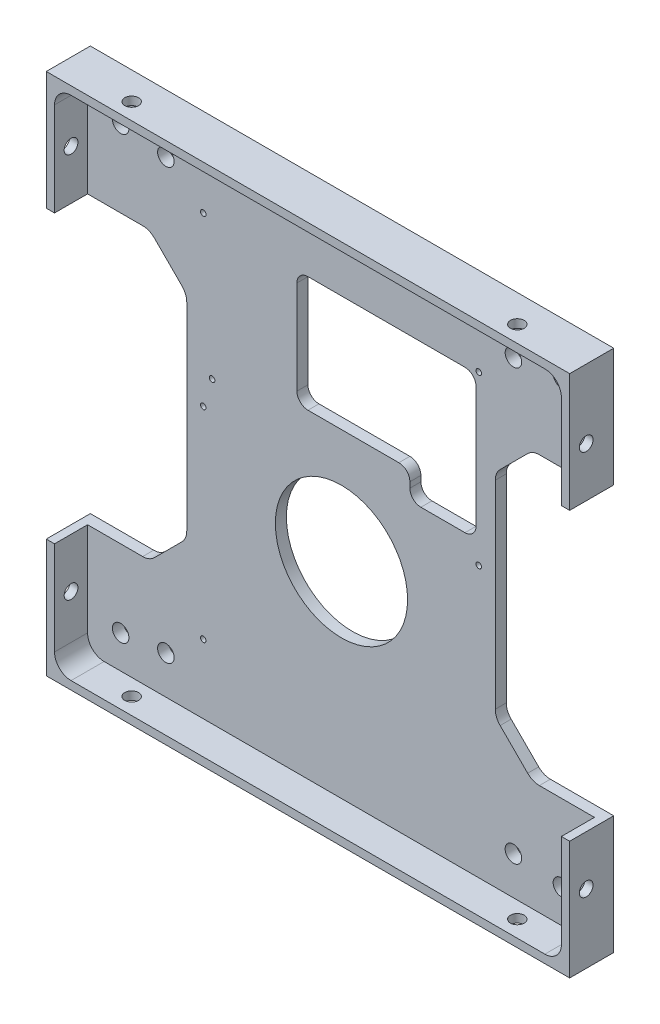
SolidWorks part; units mm, degrees
material "6061-T6 (SS)"
ref_plane "Front" through (0, 0, 0) normal (0, 0, 1) x (1, 0, 0)
ref_plane "Top" through (0, 0, 0) normal (0, 1, 0) x (1, 0, 0)
ref_plane "Right" through (0, 0, 0) normal (1, 0, 0) x (0, 0, -1)
sketch "Sketch1" plane through (0, 0, 0) normal (0, 0, 1) x (1, 0, 0)
  line L1 (-48, -48) -> (48, -48)
  line L2 (-48, -48) -> (-48, 48)
  line L3 (-48, 48) -> (48, 48)
  line L4 (48, -48) -> (48, 48)
  line L5 (-48, -48) -> (48, 48) construction
  line L6 (-48, 48) -> (48, -48) construction
  point P0 (0, 0)
  dimension "D1" = 96
  dimension "D2" = 96
extrude "Boss-Extrude1" add sketch "Sketch1" along normal blind 8
sketch "Sketch2" plane through (0, 0, 8) normal (0, 0, 1) x (1, 0, 0)
  line L1 (46, -46) -> (-46, -46)
  line L2 (46, -46) -> (46, 46)
  line L3 (46, 46) -> (-46, 46)
  line L4 (-46, -46) -> (-46, 46)
  line L5 (46, -46) -> (-46, 46) construction
  line L6 (46, 46) -> (-46, -46) construction
  point P0 (0, 0)
  dimension "D1" = 92
  dimension "D2" = 92
extrude "Component Platform" cut sketch "Sketch2" against normal blind 6
sketch "Sketch3" plane through (0, 0, 2) normal (0, 0, 1) x (1, 0, 0)
  line L1 (-33.8787, -25.1213) -> (-28.8787, -20.1213)
  line L2 (-33.8787, 25.1213) -> (-28.8787, 20.1213)
  line L3 (-28, -18) -> (-28, 18)
  line L4 (-48, -26) -> (-36, -26)
  line L7 (-48, 48) -> (-48, -48) construction
  line L8 (0, -56.7987) -> (0, 73.4321) construction
  line L9 (46, -46) -> (-57.8147, 57.8147) construction
  line L18 (46, 46) -> (-68.5705, -68.5705) construction
  line L23 (-48, 26) -> (-36, 26)
  line L26 (-48, -26) -> (-48, 26)
  line L28 (-48, -48) -> (48, -48) construction
  line L29 (48, -26) -> (48, 26)
  line L30 (48, 26) -> (36, 26)
  line L31 (33.8787, 25.1213) -> (28.8787, 20.1213)
  line L32 (28, -18) -> (28, 18)
  line L33 (33.8787, -25.1213) -> (28.8787, -20.1213)
  line L34 (48, -26) -> (36, -26)
  arc A3 (-28.8787, -20.1213) -> (-28, -18) centre (-31, -18) ccw
  arc A4 (-28.8787, 20.1213) -> (-28, 18) centre (-31, 18) cw
  arc A13 (-33.8787, -25.1213) -> (-36, -26) centre (-36, -23) cw
  arc A15 (-33.8787, 25.1213) -> (-36, 26) centre (-36, 23) ccw
  arc A17 (33.8787, 25.1213) -> (36, 26) centre (36, 23) cw
  arc A18 (28.8787, 20.1213) -> (28, 18) centre (31, 18) ccw
  arc A19 (28.8787, -20.1213) -> (28, -18) centre (31, -18) cw
  arc A20 (33.8787, -25.1213) -> (36, -26) centre (36, -23) ccw
  point P0 (-48, 0)
  point P37 (-48, 0)
  dimension "D2" = 3
  dimension "D3" = 3
  dimension "D4" = 20
  dimension "D6" = 3
  dimension "D7" = 3
  dimension "D8" = 135
  dimension "D5" = 52
  dimension "D9" = 135
  dimension "D10" = 12
  dimension "D11" = 12
  dimension "D12" = 48
extrude "Cable Slots" cut sketch "Sketch3" against normal mid plane 12
ref_plane "Center Y-Plane" through (0, 0, 0) normal (1, 0, 0) x (0, 0, -1)
ref_plane "Center X-Plane" through (0, 0, 0) normal (0, -1, 0) x (-1, 0, 0)
fillet "Inner Corner Fillets" radius 3 4 edges at (46, -46, 5) (-46, -46, 5) (46, 46, 5) (-46, 46, 5)
sketch "Sketch7" plane through (0, 0, 2) normal (0, 0, 1) x (1, 0, 0)
  line L0 (-48, -48) -> (48, -48) construction
  line L4 (48, -48) -> (48, -26) construction
  line L5 (48, 26) -> (48, 48) construction
  line L7 (48, 48) -> (-48, 48) construction
  line L8 (-43, -46) -> (43, -46) construction
  point P1 (-19.32, -29.75)
  point P4 (24.78, -32.85)
  point P5 (24.78, 32.85)
  point P8 (-22.92, 32.85)
  point P12 (24.7, -56.85)
  point P13 (24.7, 48)
  point P14 (-19.4, -48)
  point P15 (48, -32.85)
  point P16 (-48, -32.85)
  point P18 (-19.4, 48)
  point P19 (48, -32.85)
  point P20 (-48, -32.85)
  point P24 (48, 43.7)
  point P25 (-48.7506, 43.7)
  point P27 (48, 32.85)
  point P28 (-23, -48)
  point P29 (-23, 48)
  point P31 (-48.7506, 32.85)
  dimension "D1" = 16.25
  dimension "D2" = 47.7
  dimension "D3" = 15.15
  dimension "D4" = 23.22
  dimension "D5" = 23.22
  dimension "D6" = 44.1
  dimension "D7" = 15.15
  dimension "D8" = 15.15
sketch "Sketch9" plane through (0, 0, 2) normal (0, 0, 1) x (1, 0, 0)
  line L0 (24.5, 31) -> (24.5, 9)
  line L1 (22.5, 33) -> (-6, 33)
  line L2 (22.5, 7) -> (14.5, 7)
  line L5 (-8, 14) -> (-8, 31)
  line L6 (48, 26) -> (48, 48) construction
  line L7 (12.5, 9) -> (12.5, 10)
  line L8 (48, 48) -> (-48, 48) construction
  line L9 (10.5, 12) -> (-6, 12)
  arc A1 (24.5, 9) -> (22.5, 7) centre (22.5, 9) cw
  arc A2 (24.5, 31) -> (22.5, 33) centre (22.5, 31) ccw
  arc A3 (-6, 33) -> (-8, 31) centre (-6, 31) ccw
  arc A8 (-8, 14) -> (-6, 12) centre (-6, 14) ccw
  arc A9 (12.5, 10) -> (10.5, 12) centre (10.5, 10) ccw
  arc A10 (14.5, 7) -> (12.5, 9) centre (14.5, 9) cw
  point P15 (24.5, 33)
  point P18 (-8, 12)
  dimension "D1" = 2
  dimension "D6" = 2
  dimension "D7" = 8
  dimension "D8" = 32.5
  dimension "D2" = 26
  dimension "D3" = 28.5
  dimension "D4" = 15
  dimension "D5" = 23.5
  dimension "D9" = 19
sketch "Sketch11" plane through (48, 0, 0) normal (1, 0, 0) x (0, 0, -1)
  line L0 (-5, -48) -> (-5, 48) construction
  line L1 (-8, -48) -> (0, -48) construction
  line L2 (-8, 48) -> (0, 48) construction
  line L3 (-8, -48) -> (-8, -26) construction
  dimension "D1" = 3
sketch "Sketch12" plane through (0, 48, 0) normal (0, 1, 0) x (1, 0, 0)
  line L0 (-48, -5) -> (48, -5) construction
  line L1 (-48, -8) -> (-48, 0) construction
  line L2 (48, -8) -> (48, 0) construction
  line L3 (48, -8) -> (-48, -8) construction
  dimension "D1" = 3
hole_wizard "M3x0.5 Tapped Hole1" positions "Sketch13" profile "Sketch14" tap size "M3x0.5" standard "ANSI Metric"
sketch "Sketch13" plane through (48, 0, 0) normal (1, 0, 0) x (0, 0, -1)
  line L0 (-5, -48) -> (-5, 48) construction
  point P0 (-5, -35)
  point P4 (-5, 35)
  dimension "D1" = 70
  dimension "D2" = 35
sketch "Sketch14" plane through (48, -35, 5) normal (0, 1, 0) x (0, 0, -1)
  line L0 (0, 0) -> (0, 10.7511)
  line L1 (0, 10.7511) -> (1.25, 10)
  line L2 (1.25, 10) -> (1.25, 0)
  line L5 (1.25, 0) -> (0, 0)
  line L10 (0, 10.7511) -> (-1.25, 10) construction
  line L11 (0, -6.35) -> (0, 107.95) construction
  dimension "Tap Drill Dia." = 2.5
  dimension "Tap Drill Depth" = 10
  dimension "Drill Angle" = 118
hole_wizard "M3x0.5 Tapped Hole2" positions "Sketch15" profile "Sketch16" tap size "M3x0.5" standard "ANSI Metric"
sketch "Sketch15" plane through (0, 48, 0) normal (0, 1, 0) x (1, 0, 0)
  line L0 (-48, -5) -> (48, -5) construction
  point P0 (35, -5)
  point P4 (-35, -5)
  dimension "D1" = 70
  dimension "D2" = 35
sketch "Sketch16" plane through (35, 48, 5) normal (1, 0, 0) x (0, 0, 1)
  line L0 (0, 0) -> (0, 10.7511)
  line L1 (0, 10.7511) -> (1.25, 10)
  line L2 (1.25, 10) -> (1.25, 0)
  line L5 (1.25, 0) -> (0, 0)
  line L10 (0, 10.7511) -> (-1.25, 10) construction
  line L11 (0, -6.35) -> (0, 107.95) construction
  dimension "Tap Drill Dia." = 2.5
  dimension "Tap Drill Depth" = 10
  dimension "Drill Angle" = 118
mirror "Mirror1" about plane through (0, 0, 0) normal (1, 0, 0) of "M3x0.5 Tapped Hole1"
mirror "Mirror2" about plane through (0, 0, 0) normal (0, -1, 0) of "M3x0.5 Tapped Hole2"
sketch "Sketch22" plane through (0, 0, 2) normal (0, 0, 1) x (1, 0, 0)
  line L2 (46, -43) -> (46, -26) construction
  line L3 (-43, -46) -> (43, -46) construction
  line L4 (-46, -26) -> (-46, -43) construction
  line L6 (46, 26) -> (46, 43) construction
  line L7 (43, 46) -> (-43, 46) construction
  line L8 (-46, 43) -> (-46, 26) construction
  point P0 (-31.791, -39.06)
  point P1 (-31.791, 38.94)
  point P2 (31.29, 38.94)
  point P3 (31.29, -39.06)
  dimension "D1" = 14.71
  dimension "D2" = 6.94
  dimension "D3" = 6.94
  dimension "D4" = 14.209
  dimension "D5" = 14.71
  dimension "D6" = 7.06
  dimension "D7" = 7.06
  dimension "D8" = 14.209
sketch "Sketch29" plane through (0, 0, 0) normal (0, 0, -1) x (-1, 0, 0)
  line L0 (28, 18) -> (28, -18) construction
  line L2 (48, -48) -> (-48, -48) construction
  circle A0 centre (-0.0819, -8.7479) radius 12
  dimension "D1" = 24
  dimension "D2" = 28.0819
  dimension "D3" = 39.2521
extrude "HDD Extrusion Cutout" cut sketch "Sketch29" against normal blind 10
extrude "HDD Extrusion Cutout 2" cut sketch "Sketch9" against normal blind 10
hole_wizard "Ø3.0mm Dowel Hole1" positions "Sketch30" profile "Sketch31" hole size "Ø3.0" standard "ANSI Metric" end condition up to next
sketch "Sketch30" plane through (0, 0, 2) normal (0, 0, 1) x (1, 0, 0)
  point P0 (-31.791, -39.06)
  point P3 (31.29, -39.06)
  point P6 (31.29, 38.94)
  point P9 (-31.791, 38.94)
sketch "Sketch31" plane through (-31.791, -39.06, 2) normal (1, 0, 0) x (0, -1, 0)
  line L0 (0, 0) -> (0, 2)
  line L1 (0, 2) -> (1.5, 2)
  line L2 (1.5, 2) -> (1.5, 0)
  line L5 (1.5, 0) -> (0, 0)
  line L11 (0, -6.35) -> (0, 107.95) construction
  dimension "Thru Hole Dia." = 3
  dimension "Thru Hole Depth" = 2
sketch "Sketch32" plane through (0, 0, 2) normal (0, 0, 1) x (1, 0, 0)
  line L0 (0, -46) -> (0, 46) construction
  line L1 (-43, -46) -> (43, -46) construction
  line L2 (43, 46) -> (-43, 46) construction
  line L3 (48.3015, 0) -> (-47.2615, 0) construction
  line L5 (-48, -48) -> (48, -48) construction
  line L7 (40, 40) -> (-40, 40)
  line L8 (40, 40) -> (40, -40)
  line L9 (40, -40) -> (-40, -40)
  line L10 (-40, 40) -> (-40, -40)
  line L11 (40, 40) -> (-40, -40) construction
  line L12 (40, -40) -> (-40, 40) construction
  point P8 (0, 0)
  dimension "D1" = 48
  dimension "D2" = 80
  dimension "D3" = 80
hole_wizard "Ø3.0mm Dowel Hole2" positions "Sketch33" profile "Sketch34" hole size "Ø3.0" standard "ANSI Metric" end condition through all
sketch "Sketch33" plane through (0, 0, 2) normal (0, 0, 1) x (1, 0, 0)
  point P0 (40, -40)
  point P3 (-40, -40)
  point P6 (-40, 40)
  point P9 (40, 40)
sketch "Sketch34" plane through (40, -40, 2) normal (1, 0, 0) x (0, -1, 0)
  line L0 (0, 0) -> (0, 2)
  line L1 (0, 2) -> (1.5, 2)
  line L2 (1.5, 2) -> (1.5, 0)
  line L5 (1.5, 0) -> (0, 0)
  line L11 (0, -6.35) -> (0, 107.95) construction
  dimension "Thru Hole Dia." = 3
  dimension "Thru Hole Depth" = 2
sketch "Sketch35" plane through (0, 0, 0) normal (0, 0, -1) x (-1, 0, 0)
  line L1 (-47.5, 47.5) -> (47.5, 47.5)
  line L2 (-47.5, 47.5) -> (-47.5, -47.5)
  line L3 (-47.5, -47.5) -> (47.5, -47.5)
  line L4 (47.5, 47.5) -> (47.5, -47.5)
  line L5 (-47.5, 47.5) -> (47.5, -47.5) construction
  line L6 (-47.5, -47.5) -> (47.5, 47.5) construction
  point P0 (0, 0)
  dimension "D1" = 95
extrude "Cut-Extrude1" cut sketch "Sketch35" against normal up to next flip side to cut
sketch "Sketch36" plane through (0, 0, 2) normal (0, 0, 1) x (1, 0, 0)
  line L1 (-43, -46) -> (-43, 46) construction
  line L2 (-43, -46) -> (43, -46) construction
  point P19 (-25, 3.1)
  point P20 (-23.4, 8.2)
  point P21 (-25, 33.5)
  point P22 (-25, -33.5)
  point P23 (25, 33.5)
  point P24 (25, 3.1)
  dimension "D1" = 12.5
  dimension "D2" = 18
  dimension "D3" = 49.1
  dimension "D4" = 54.2
  dimension "D5" = 18
  dimension "D6" = 19.6
  dimension "D7" = 18
  dimension "D8" = 79.5
  dimension "D9" = 49.1
  dimension "D10" = 79.5
  dimension "D11" = 68
  dimension "D12" = 68
hole_wizard "M1.6 Clearance Hole2" positions "3DSketch1" profile "Sketch43" hole size "M1.6" standard "ANSI Metric" end condition through all
sketch3d "3DSketch1"
  point P0 (-25, -33.5, 2)
  point P3 (-25, 3.1, 2)
  point P6 (-23.4, 8.2, 2)
  point P9 (-25, 33.5, 2)
  point P12 (25, 33.5, 2)
  point P15 (25, 3.1, 2)
sketch "Sketch43" plane through (-25, -33.5, 2) normal (1, 0, 0) x (0, -1, 0)
  line L0 (0, 0) -> (0, 2)
  line L1 (0, 2) -> (0.5, 2)
  line L2 (0.5, 2) -> (0.5, 0)
  line L5 (0.5, 0) -> (0, 0)
  line L11 (0, -6.35) -> (0, 107.95) construction
  dimension "Thru Hole Dia." = 1
  dimension "Thru Hole Depth" = 2
equation "\"MountingBracketXYSideTolerance\"= - 0.5"
equation "\"D1@Sketch35\"=96+\"MountingBracketXYSideTolerance\"*2"
